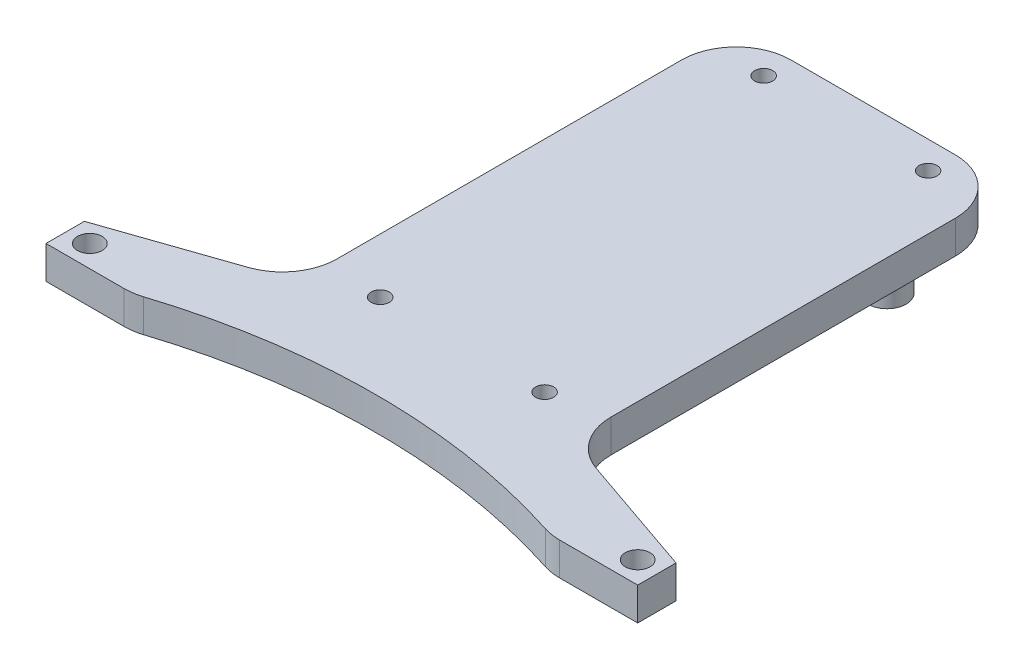
SolidWorks part; units mm, degrees
ref_plane "Front Plane" through (0, 0, 0) normal (0, 0, 1) x (1, 0, 0)
ref_plane "Top Plane" through (0, 0, 0) normal (0, 1, 0) x (1, 0, 0)
ref_plane "Right Plane" through (0, 0, 0) normal (1, 0, 0) x (0, 0, -1)
sketch "Sketch1" plane through (0, 0, 0) normal (0, 1, 0) x (1, 0, 0)
  line L0 (4, 3) -> (104, 3) construction
  line L1 (0, 0) -> (108, 0)
  line L2 (0, 0) -> (0, 6)
  line L4 (108, 0) -> (108, 6)
  line L5 (54, 16) -> (54, 0) construction
  line L6 (0, 6) -> (29, 16)
  line L7 (29, 16) -> (79, 16) construction
  line L8 (79, 16) -> (108, 6)
  line L9 (29, 16) -> (29, 96)
  line L10 (29, 96) -> (79, 96)
  line L11 (79, 96) -> (79, 16)
  line L12 (39, 21) -> (39, 91) construction
  line L13 (39, 91) -> (69, 91) construction
  line L14 (69, 91) -> (69, 21) construction
  line L15 (69, 21) -> (39, 21) construction
  line L16 (39, 21) -> (69, 91) construction
  circle A0 centre (4, 3) radius 2.25
  circle A1 centre (104, 3) radius 2.25
  circle A2 centre (39, 91) radius 1.65
  circle A3 centre (69, 91) radius 1.65
  circle A4 centre (39, 21) radius 1.65
  circle A5 centre (69, 21) radius 1.65
  point P10 (54, 0)
  point P11 (54, 3)
  point P17 (54, 16)
  point P26 (54, 91)
  point P27 (54, 96)
  dimension "D2" = 3
  dimension "D3" = 4.5
  dimension "D8" = 30
  dimension "D12" = 3.3
  dimension "D1" = 108
  dimension "D4" = 100
  dimension "D5" = 6
  dimension "D6" = 16
  dimension "D7" = 50
  dimension "D9" = 70
  dimension "D10" = 80
  dimension "D11" = 5
extrude "Boss-Extrude1" add sketch "Sketch1" along normal blind 6
sketch "Sketch2" plane through (0, 6, 0) normal (0, 1, 0) x (1, 0, 0)
  line L0 (19, 0) -> (89, 0)
  line L1 (0, 0) -> (108, 0) construction
  line L2 (79, 96) -> (29, 96) construction
  arc A0 (19, 0) -> (89, 0) centre (54, -114.7824) cw
  point P0 (54, 96)
  point P5 (54, 0)
  dimension "D2" = 120
  dimension "D1" = 70
extrude "Cut-Extrude1" cut sketch "Sketch2" against normal through all both and the other way through all
sketch "Sketch3" plane through (0, 0, 0) normal (0, -1, 0) x (1, 0, 0)
  line L0 (36.5, -81) -> (71.5, -81) construction
  line L1 (79, -96) -> (29, -96) construction
  circle A0 centre (36.5, -81) radius 3.5
  circle A1 centre (71.5, -81) radius 3.5
  point P4 (54, -81)
  point P7 (54, -96)
  dimension "D1" = 7
  dimension "D2" = 35
  dimension "D3" = 15
extrude "Boss-Extrude2" add sketch "Sketch3" along normal blind 7.1
chamfer "Chamfer1" distance 2 angle 45 2 edges at (71.5, 0, -84.5) (36.5, 0, -84.5)
sketch "Sketch4" plane through (0, 6, 0) normal (0, 1, 0) x (1, 0, 0)
  line L0 (54, 96) -> (54, 5.2176) construction
  line L1 (79, 96) -> (29, 96) construction
  line L2 (0, 0) -> (0, -1)
  line L3 (0, -1) -> (15.8744, -1)
  line L5 (0, 0) -> (19, 0) construction
  line L6 (19, 0) -> (0, 0)
  line L7 (0, 0) -> (19, 0) construction
  line L8 (108, -1) -> (92.1256, -1)
  line L9 (108, 0) -> (108, -1)
  line L10 (89, 0) -> (108, 0)
  arc A0 (89, 0) -> (19, 0) centre (54, -114.7824) ccw construction
  arc A2 (89, 0) -> (19, 0) centre (54, -114.7824) ccw construction
  arc A3 (92.1256, -1) -> (89, 0) centre (54, -114.7824) ccw
  arc A4 (15.8744, -1) -> (19, 0) centre (54, -114.7824) cw
  point P17 (19, 0)
  dimension "D1" = 1
extrude "Boss-Extrude3" add sketch "Sketch4" against normal up to surface (6 mm away) up to face at (71.5, 0, -86.5)
fillet "Fillet1" radius 10 6 edges at (79, 3, -96) (29, 3, -96) (79, 3, -16) (29, 3, -16) (92.1256, 3, 1) (15.8744, 3, 1)
